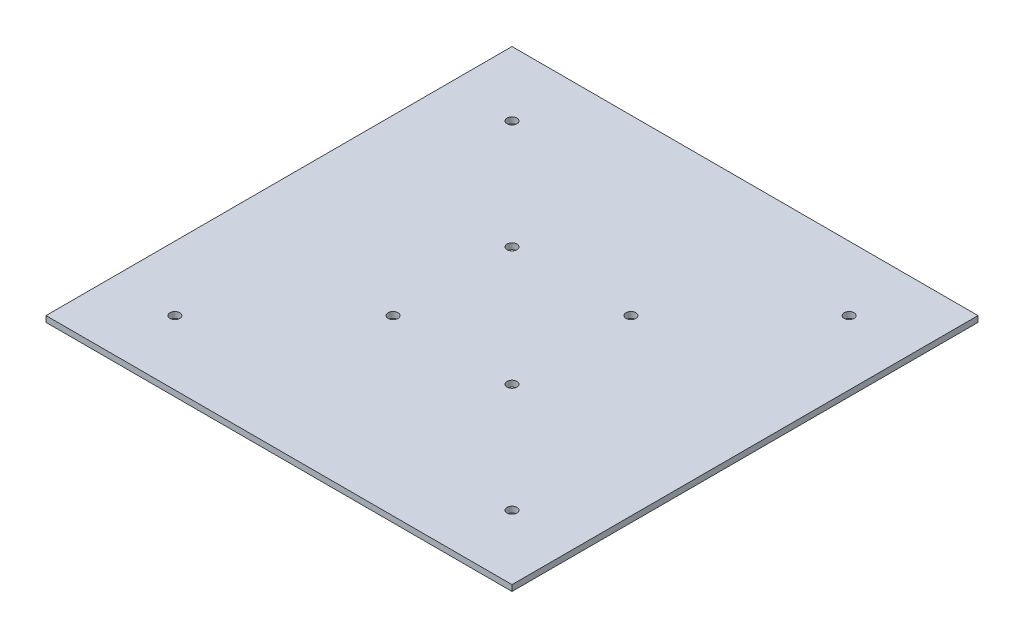
SolidWorks part; units mm, degrees
ref_plane "Front Plane" through (0, 0, 0) normal (0, 0, 1) x (1, 0, 0)
ref_plane "Top Plane" through (0, 0, 0) normal (0, 1, 0) x (1, 0, 0)
ref_plane "Right Plane" through (0, 0, 0) normal (1, 0, 0) x (0, 0, -1)
sketch "Sketch1" plane through (0, 0, 0) normal (0, 1, 0) x (1, 0, 0)
  line L1 (0, 0) -> (235, 0)
  line L2 (0, 0) -> (0, 235)
  line L3 (0, 235) -> (235, 235)
  line L4 (235, 0) -> (235, 235)
  dimension "D1" = 235
extrude "Boss-Extrude1" add sketch "Sketch1" along normal blind 3
sketch "Sketch2" plane through (0, 3, 0) normal (0, 1, 0) x (1, 0, 0)
  line L0 (117.5, 235) -> (117.5, 0) construction
  line L1 (235, 235) -> (0, 235) construction
  line L2 (0, 0) -> (235, 0) construction
  line L3 (0, 117.5) -> (235, 117.5) construction
  line L4 (0, 235) -> (0, 0) construction
  line L5 (235, 0) -> (235, 235) construction
  circle A0 centre (32.5, 202.5) radius 2.5
  circle A3 centre (202.5, 202.5) radius 2.5
  circle A4 centre (202.5, 32.5) radius 2.5
  circle A7 centre (32.5, 32.5) radius 2.5
  circle A8 centre (87.5, 147.5) radius 2.5
  circle A9 centre (147.5, 147.5) radius 2.5
  circle A10 centre (147.5, 87.5) radius 2.5
  circle A11 centre (87.5, 87.5) radius 2.5
  dimension "D1" = 5
  dimension "D2" = 60
  dimension "D4" = 60
  dimension "D5" = 170
  dimension "D3" = 170
extrude "Cut-Extrude1" cut sketch "Sketch2" against normal up to next
